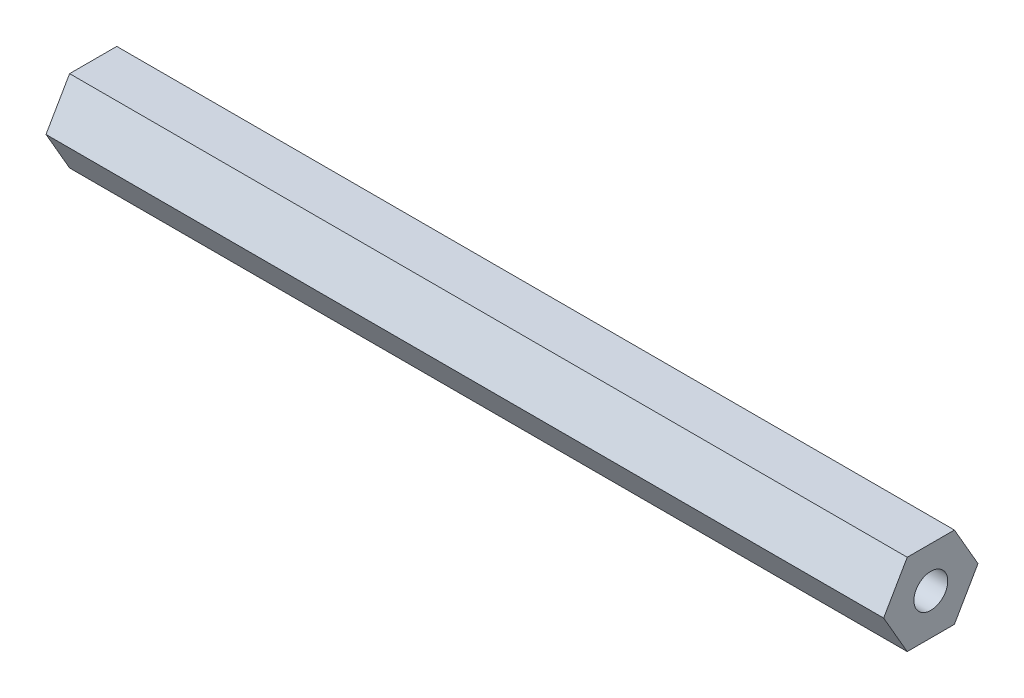
SolidWorks part; units mm, degrees
material "6061-T6 (SS)"
ref_plane "Front Plane" through (0, 0, 0) normal (0, 0, 1) x (1, 0, 0)
ref_plane "Top Plane" through (0, 0, 0) normal (0, 1, 0) x (1, 0, 0)
ref_plane "Right Plane" through (0, 0, 0) normal (1, 0, 0) x (0, 0, -1)
sketch "Sketch1" plane through (0, 0, 0) normal (1, 0, 0) x (0, 0, -1)
  line L1 (3.6662, 6.35) -> (-3.6662, 6.35)
  line L2 (-3.6662, 6.35) -> (-7.3323, 0)
  line L3 (-7.3323, 0) -> (-3.6662, -6.35)
  line L4 (-3.6662, -6.35) -> (3.6662, -6.35)
  line L5 (3.6662, -6.35) -> (7.3323, 0)
  line L6 (7.3323, 0) -> (3.6662, 6.35)
  circle A0 centre (0, 0) radius 6.35 construction
  circle A1 centre (0, 0) radius 2.6289
  dimension "D1" = 5.2578
  dimension "D2" = 12.7
extrude "Boss-Extrude1" add sketch "Sketch1" along normal blind 130.175
